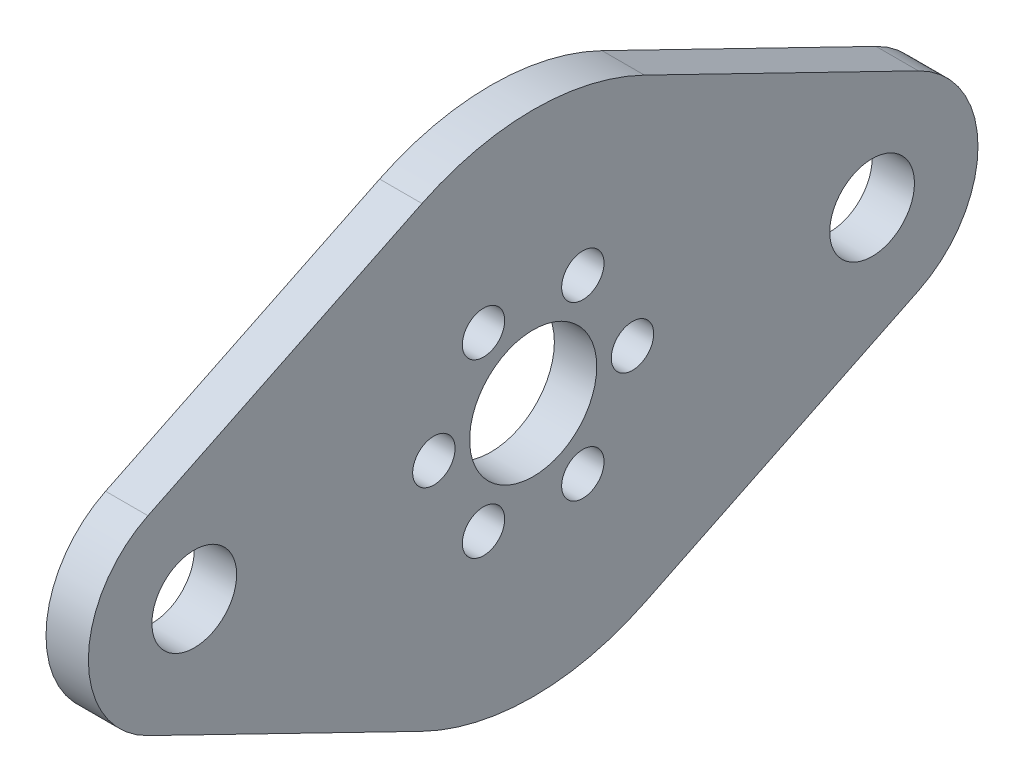
SolidWorks part; units mm, degrees
ref_plane "Front Plane" through (0, 0, 0) normal (0, 0, 1) x (1, 0, 0)
ref_plane "Top Plane" through (0, 0, 0) normal (0, 1, 0) x (1, 0, 0)
ref_plane "Right Plane" through (0, 0, 0) normal (1, 0, 0) x (0, 0, -1)
sketch "Sketch1" plane through (0, 0, 0) normal (1, 0, 0) x (0, 0, -1)
  line L0 (25.4, 0) -> (-25.4, 0) construction
  line L1 (-28.8727, 7.1375) -> (-8.3344, 17.1301)
  line L2 (8.3344, 17.1301) -> (28.8727, 7.1375)
  line L3 (28.8727, -7.1375) -> (8.3344, -17.1301)
  line L4 (-8.3344, -17.1301) -> (-28.8727, -7.1375)
  line L5 (3.7211, 6.4451) -> (-3.7211, -6.4451) construction
  circle A0 centre (0, 0) radius 4.7625
  circle A1 centre (0, 0) radius 19.05 construction
  circle A2 centre (-25.4, 0) radius 7.9375 construction
  circle A3 centre (25.4, 0) radius 7.9375 construction
  circle A4 centre (-25.4, 0) radius 3.175
  circle A5 centre (25.4, 0) radius 3.175
  arc A6 (-28.8727, 7.1375) -> (-28.8727, -7.1375) centre (-25.4, 0) ccw
  arc A7 (-8.3344, 17.1301) -> (8.3344, 17.1301) centre (0, 0) cw
  arc A8 (28.8727, 7.1375) -> (28.8727, -7.1375) centre (25.4, 0) cw
  arc A9 (8.3344, -17.1301) -> (-8.3344, -17.1301) centre (0, 0) cw
  circle A10 centre (-3.7211, -6.4451) radius 1.5875
  circle A11 centre (3.7211, 6.4451) radius 1.5875
  circle A12 centre (3.7211, -6.4451) radius 1.5875
  circle A13 centre (-3.7211, 6.4451) radius 1.5875
  circle A14 centre (-7.4422, 0) radius 1.5875
  circle A15 centre (7.4422, 0) radius 1.5875
  circle A16 centre (0, 0) radius 12.7 construction
  point P10 (0, 0)
  point P25 (0, 0)
  point P37 (0, 0)
  dimension "D1" = 9.525
  dimension "D2" = 38.1
  dimension "D4" = 6.35
  dimension "D5" = 15.875
  dimension "D7" = 3.175
  dimension "D10" = 25.4
  dimension "D3" = 50.8
  dimension "D6" = 60
  dimension "D8" = 14.8844
  dimension "D9" = 3
extrude "Boss-Extrude1" add sketch "Sketch1" along normal blind 3.175
